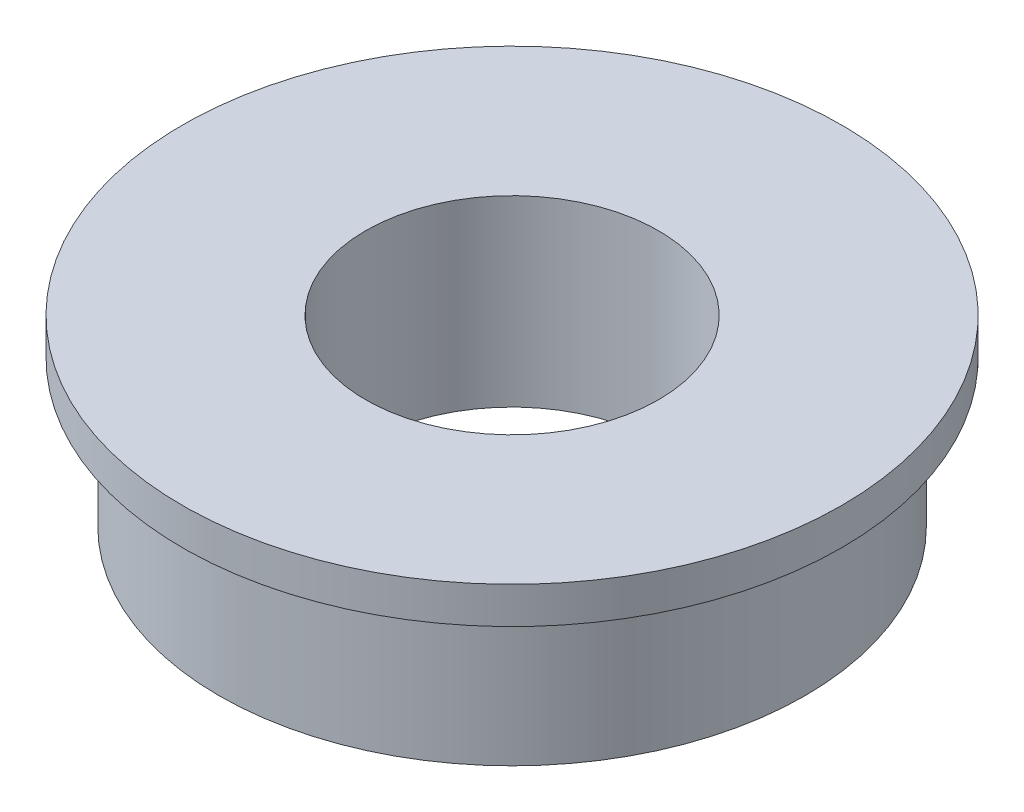
SolidWorks part; units mm, degrees
ref_plane "Front Plane" through (0, 0, 0) normal (0, 0, 1) x (1, 0, 0)
ref_plane "Top Plane" through (0, 0, 0) normal (0, 1, 0) x (1, 0, 0)
ref_plane "Right Plane" through (0, 0, 0) normal (1, 0, 0) x (0, 0, -1)
sketch "Sketch1" plane through (0, 0, 0) normal (0, 0, 1) x (1, 0, 0)
  line L0 (0, -8.4875) -> (0, 8.4875) construction
  line L2 (8, -0.6988) -> (4, -0.6988)
  line L3 (8, -0.6988) -> (8, 3.3012)
  line L4 (8, 4.3012) -> (4, 4.3012)
  line L5 (4, -0.6988) -> (4, 4.3012)
  line L6 (8, 4.3012) -> (9, 4.3012)
  line L8 (8, 3.3012) -> (9, 3.3012)
  line L9 (9, 4.3012) -> (9, 3.3012)
  point P4 (0, 0)
  dimension "D1" = 4
  dimension "D2" = 8
  dimension "D3" = 9
  dimension "D4" = 1
  dimension "D5" = 4
revolve "Revolve1" add sketch "Sketch1" angle 360 about L0
